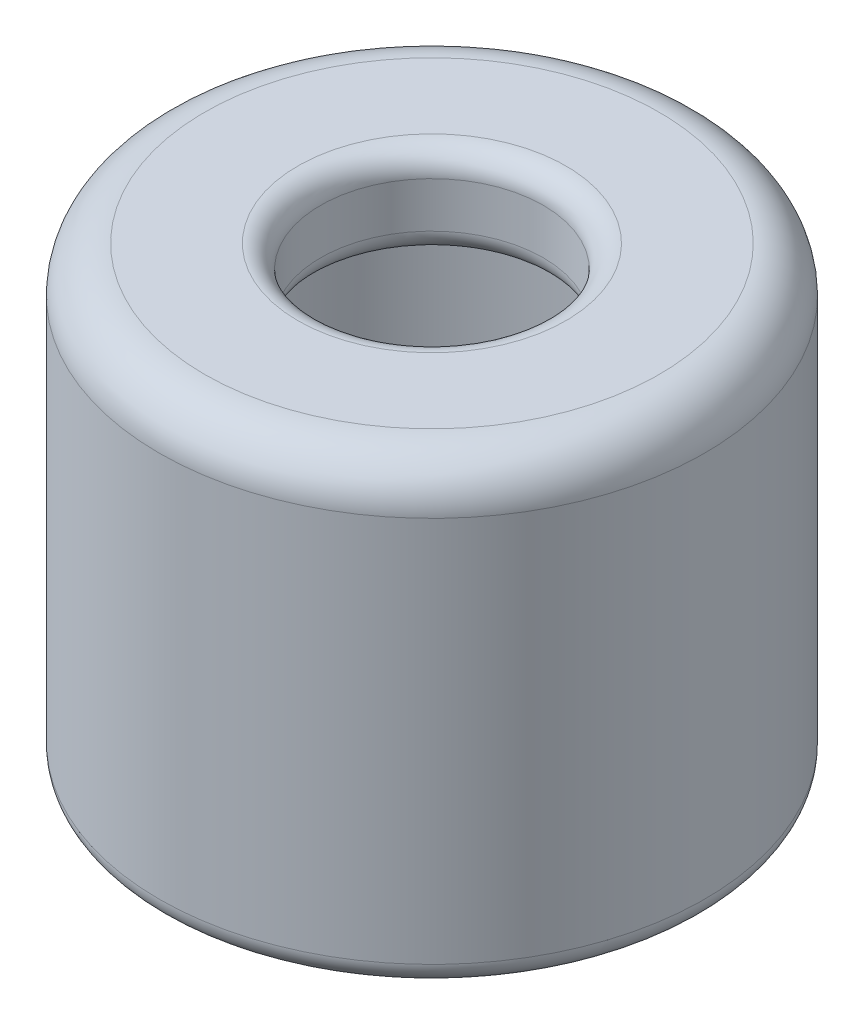
SolidWorks part; units mm, degrees
ref_plane "前视基准面" through (0, 0, 0) normal (0, 0, 1) x (1, 0, 0)
ref_plane "上视基准面" through (0, 0, 0) normal (0, 1, 0) x (1, 0, 0)
ref_plane "右视基准面" through (0, 0, 0) normal (1, 0, 0) x (0, 0, -1)
sketch "草图5" plane through (0, 0, 0) normal (0, 1, 0) x (1, 0, 0)
  circle A0 centre (0, 0) radius 6
  circle A1 centre (0, 0) radius 2.45
  dimension "D1" = 12
  dimension "D2" = 4.9
extrude "凸台-拉伸1" add sketch "草图5" along normal blind 10
sketch "草图7" plane through (0, 0, 0) normal (0, -1, 0) x (1, 0, 0)
  circle A0 centre (0, 0) radius 4.5
extrude "切除-拉伸1" cut sketch "草图7" against normal blind 8
fillet "圆角1" radius 1 1 edges at (0, 10, 6)
fillet "圆角2" radius 0.5 5 edges at (0, 0, 6) (0, 0, -4.5) (0, 8, -2.45) (0, 8, -4.5) (0, 10, 2.45)
